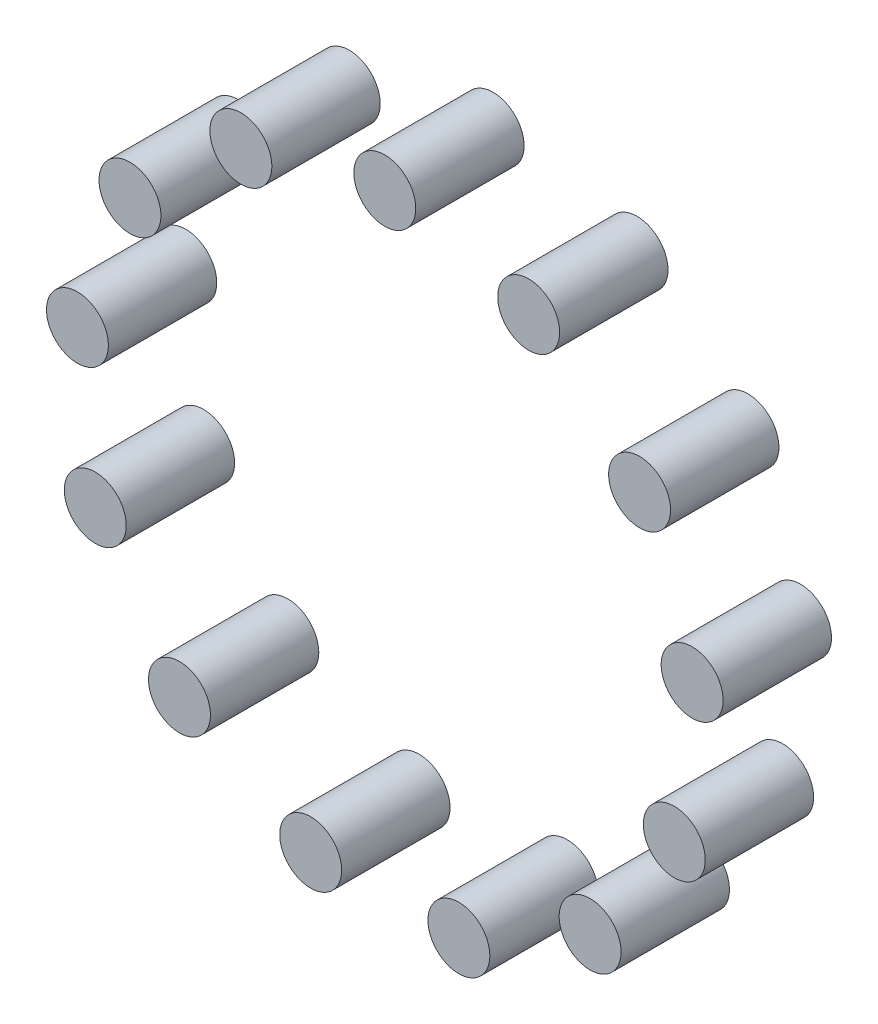
SolidWorks part; units mm, degrees
ref_plane "Front Plane" through (0, 0, 0) normal (0, 0, 1) x (1, 0, 0)
ref_plane "Top Plane" through (0, 0, 0) normal (0, 1, 0) x (1, 0, 0)
ref_plane "Right Plane" through (0, 0, 0) normal (1, 0, 0) x (0, 0, -1)
sketch "Sketch1" plane through (0, 0, 0) normal (0, 0, 1) x (1, 0, 0)
  circle A0 centre (0, 0) radius 40 construction
  circle A1 centre (0, 40) radius 4
  circle A2 centre (18.5889, 35.4182) radius 4
  circle A3 centre (32.9194, 22.7226) radius 4
  circle A4 centre (39.7084, 4.8215) radius 4
  circle A5 centre (37.4006, -14.1842) radius 4
  circle A6 centre (26.5249, -29.9404) radius 4
  circle A7 centre (9.5726, -38.8377) radius 4
  circle A8 centre (-9.5726, -38.8377) radius 4
  circle A9 centre (-26.5249, -29.9404) radius 4
  circle A10 centre (-37.4006, -14.1842) radius 4
  circle A11 centre (-39.7084, 4.8215) radius 4
  circle A12 centre (-32.9194, 22.7226) radius 4
  circle A13 centre (-18.5889, 35.4182) radius 4
  point P32 (0, 0)
  dimension "D1" = 8
  dimension "D3" = 80
  dimension "D2" = 13
extrude "Boss-Extrude1" add sketch "Sketch1" along normal blind 14 contours A13
